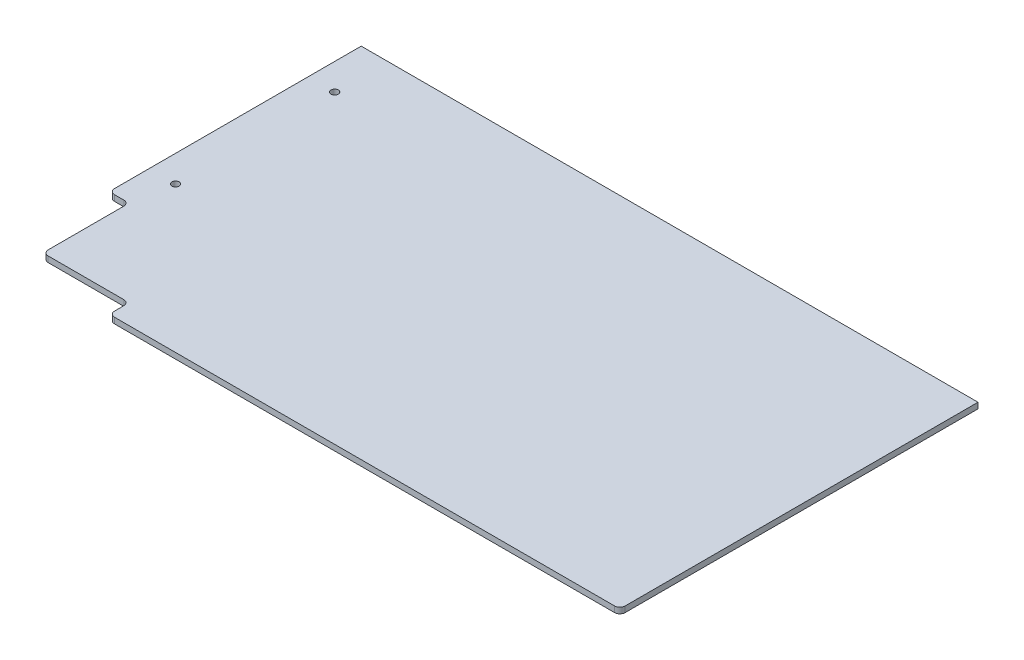
SolidWorks part; units mm, degrees
ref_plane "Front Plane" through (0, 0, 0) normal (0, 0, 1) x (1, 0, 0)
ref_plane "Top Plane" through (0, 0, 0) normal (0, 1, 0) x (1, 0, 0)
ref_plane "Right Plane" through (0, 0, 0) normal (1, 0, 0) x (0, 0, -1)
sketch "Sketch1" plane through (0, 0, 0) normal (0, 1, 0) x (1, 0, 0)
  line L1 (0, 0) -> (304.8, 0)
  line L2 (0, 0) -> (0, 190.5)
  line L3 (0, 190.5) -> (304.8, 190.5)
  line L4 (304.8, 0) -> (304.8, 190.5)
  dimension "D1" = 190.5
  dimension "D2" = 304.8
extrude "Boss-Extrude1" add sketch "Sketch1" along normal blind 2.7781
sketch "Sketch2" plane through (0, 2.7781, 0) normal (0, 1, 0) x (1, 0, 0)
  line L0 (304.8, 0) -> (304.8, 190.5) construction
  line L1 (0, 0) -> (304.8, 0)
  line L2 (0, 0) -> (0, 19.05)
  line L3 (0, 19.05) -> (304.8, 19.05)
  line L4 (304.8, 0) -> (304.8, 19.05)
  dimension "D2" = 19.05
extrude "Cut-Extrude1" cut sketch "Sketch2" against normal through all
sketch "Sketch3" plane through (0, 2.7781, 0) normal (0, 1, 0) x (1, 0, 0)
  line L5 (0, 190.5) -> (0, 19.05) construction
  line L6 (0, 19.05) -> (0, 69.85)
  line L11 (0, 69.85) -> (9.525, 69.85)
  line L12 (9.525, 69.85) -> (9.525, 28.575)
  line L13 (9.525, 28.575) -> (50.8, 28.575)
  line L14 (50.8, 28.575) -> (50.8, 19.05)
  line L15 (304.8, 19.05) -> (0, 19.05) construction
  line L16 (50.8, 19.05) -> (0, 19.05)
  dimension "D5" = 50.8
  dimension "D6" = 50.8
  dimension "D7" = 9.525
  dimension "D8" = 9.525
extrude "Cut-Extrude2" cut sketch "Sketch3" against normal through all
sketch "Sketch4" plane through (0, 2.7781, 0) normal (0, 1, 0) x (1, 0, 0)
  line L0 (304.8, 19.05) -> (50.8, 19.05) construction
  line L1 (0, 190.5) -> (0, 69.85) construction
  circle A0 centre (12.7, 165.1) radius 1.7526
  circle A1 centre (12.7, 88.9) radius 1.7526
  dimension "D1" = 3.5052
  dimension "D4" = 12.7
  dimension "D2" = 76.2
  dimension "D3" = 69.85
extrude "Cut-Extrude3" cut sketch "Sketch4" against normal through all
sketch "Sketch5" plane through (0, 2.7781, 0) normal (0, 1, 0) x (1, 0, 0)
  line L0 (304.8, 19.05) -> (50.8, 19.05) construction
  line L1 (304.8, 190.5) -> (295.275, 190.5)
  line L2 (304.8, 190.5) -> (304.8, 19.05)
  line L3 (304.8, 19.05) -> (295.275, 19.05)
  line L4 (295.275, 190.5) -> (295.275, 19.05)
  line L5 (304.8, 190.5) -> (0, 190.5) construction
  dimension "D1" = 9.525
extrude "Cut-Extrude4" cut sketch "Sketch5" against normal through all
fillet "Fillet1" radius 2.54 6 edges at (295.275, 1.3891, -19.05) (50.8, 1.3891, -19.05) (50.8, 1.3891, -28.575) (9.525, 1.3891, -69.85) (9.525, 1.3891, -28.575) (0, 1.3891, -69.85)
